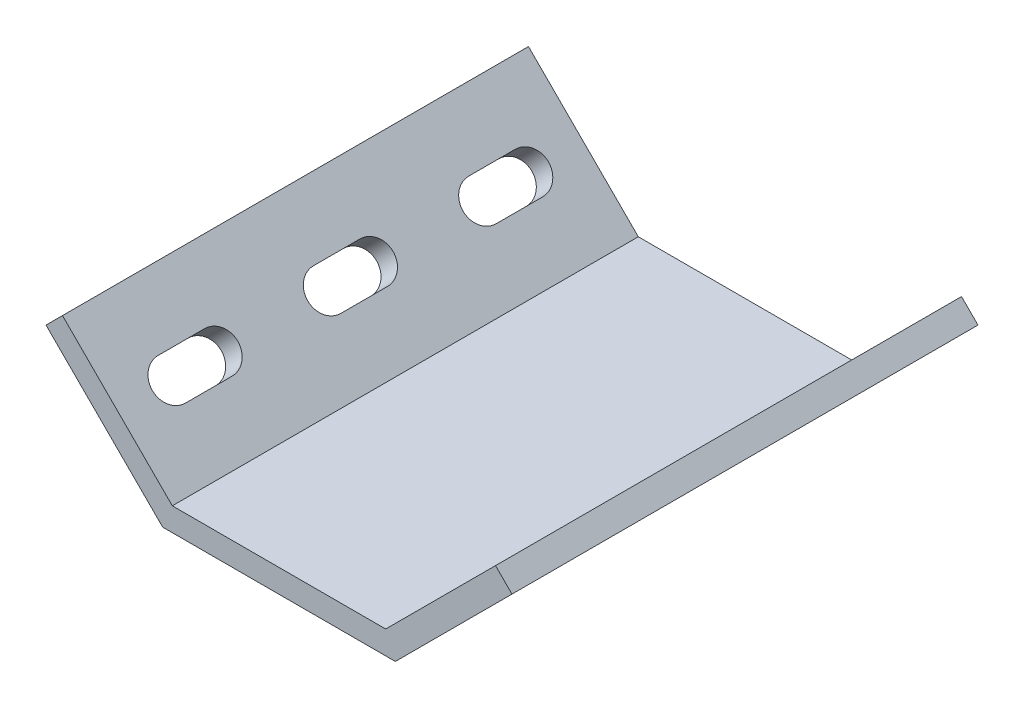
SolidWorks part; units mm, degrees
material "Алюминий"
ref_plane "Спереди" through (0, 0, 0) normal (0, 0, 1) x (1, 0, 0)
ref_plane "Сверху" through (0, 0, 0) normal (0, 1, 0) x (1, 0, 0)
ref_plane "Справа" through (0, 0, 0) normal (1, 0, 0) x (0, 0, -1)
sketch "Эскиз1" plane through (0, 0, 0) normal (0, 0, 1) x (1, 0, 0)
  line L0 (-13.7365, 0) -> (13.7365, 0)
  line L1 (13.7365, 0) -> (27.8787, 14.1421)
  line L2 (0, 0) -> (0, 29.6898) construction
  line L3 (-13.7365, 0) -> (-27.8787, 14.1421)
  line L4 (13.7365, 0) -> (-0.4056, 14.1421) construction
  line L5 (-0.4056, 14.1421) -> (13.7365, 28.2843) construction
  line L6 (13.7365, 28.2843) -> (27.8787, 14.1421) construction
  line L7 (-27.8787, 14.1421) -> (-13.7365, 28.2843) construction
  line L8 (-13.7365, 28.2843) -> (0.4056, 14.1421) construction
  line L9 (0.4056, 14.1421) -> (-13.7365, 0) construction
  line L10 (-27.8787, 14.1421) -> (-30, 12.0208) construction
  line L11 (27.8787, 14.1421) -> (30, 12.0208) construction
  dimension "D1" = 90
  dimension "D2" = 20
  dimension "D3" = 3
  dimension "D4" = 55.7574
  dimension "D5" = 60
extrude "Вытянуть-Тонкостенный1" add sketch "Эскиз1" along normal blind 20 thin
sketch "Эскиз2" plane through (-6.8683, -6.8683, 0) normal (0.7071, 0.7071, 0) x (0, 0, -1)
  line L0 (-7, 19.7132) -> (-13, 19.7132) construction
  line L1 (-7, 17.2132) -> (-13, 17.2132)
  line L2 (-7, 22.2132) -> (-13, 22.2132)
  line L3 (-10, 19.7132) -> (-10, 9.7132) construction
  line L4 (-20, 9.7132) -> (0, 9.7132) construction
  line L5 (-10, 19.7132) -> (-10, 29.7132) construction
  line L6 (-20, 29.7132) -> (0, 29.7132) construction
  arc A0 (-7, 17.2132) -> (-7, 22.2132) centre (-7, 19.7132) ccw
  arc A1 (-13, 22.2132) -> (-13, 17.2132) centre (-13, 19.7132) ccw
  point P2 (-10, 19.7132)
  dimension "D2" = 11
  dimension "D1" = 5
extrude "Вырез-Вытянуть1" cut sketch "Эскиз2" against normal through all
mirror "Зеркальное отражение1" about plane through (0, 0, 0) normal (1, 0, 0) of "Вырез-Вытянуть1"
pattern_linear "Линейный массив1" count 3 spacing 20 along (0, 0, -1) of bodies 112
combine bodies "Соединить2" operation type add bodies to combine 113 114 112
